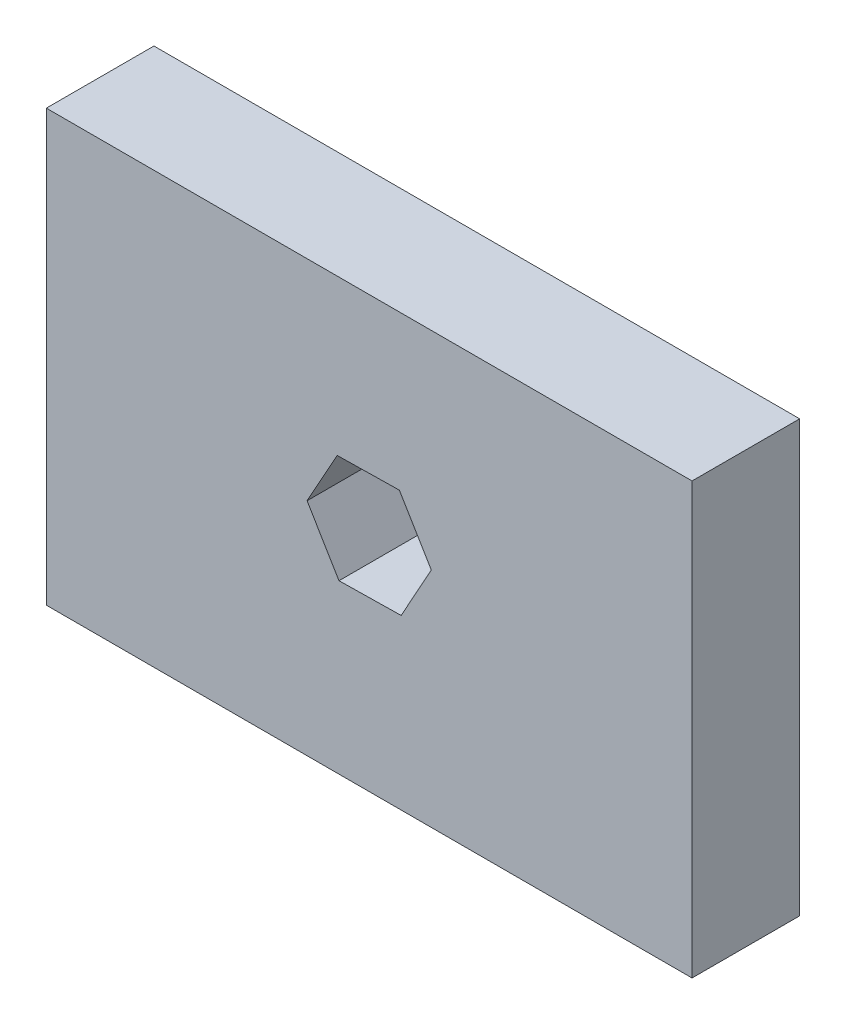
SolidWorks part; units mm, degrees
material "ALUMINUM 6061-T6"
ref_plane "Front Plane" through (0, 0, 0) normal (0, 0, 1) x (1, 0, 0)
ref_plane "Top Plane" through (0, 0, 0) normal (0, 1, 0) x (1, 0, 0)
ref_plane "Right Plane" through (0, 0, 0) normal (1, 0, 0) x (0, 0, -1)
sketch "Sketch1" plane through (0, 0, 0) normal (0, 0, 1) x (1, 0, 0)
  line L1 (-38.1, -25.4) -> (38.1, -25.4)
  line L2 (-38.1, -25.4) -> (-38.1, 25.4)
  line L3 (-38.1, 25.4) -> (38.1, 25.4)
  line L4 (38.1, -25.4) -> (38.1, 25.4)
  line L5 (-38.1, -25.4) -> (38.1, 25.4) construction
  line L6 (-38.1, 25.4) -> (38.1, -25.4) construction
  point P0 (0, 0)
  dimension "D1" = 76.2
  dimension "D2" = 50.8
extrude "Boss-Extrude1" add sketch "Sketch1" along normal mid plane 12.7
sketch "Sketch3" plane through (0, 0, 6.35) normal (0, 0, 1) x (1, 0, 0)
  line L0 (-38.1, -25.4) -> (38.1, -25.4) construction
  line L1 (-3.5621, -5.6304) -> (3.7693, -5.5108)
  line L2 (3.7693, -5.5108) -> (7.3314, 0.8982)
  line L3 (7.3314, 0.8982) -> (3.5621, 7.1875)
  line L4 (3.5621, 7.1875) -> (-3.7693, 7.0679)
  line L5 (-3.7693, 7.0679) -> (-7.3314, 0.6589)
  line L6 (-7.3314, 0.6589) -> (-3.5621, -5.6304)
  circle A0 centre (0, 0.7786) radius 6.35 construction
  dimension "D1" = 12.7
  dimension "D2" = 0.935
extrude "Cut-Extrude1" cut sketch "Sketch3" against normal through all
